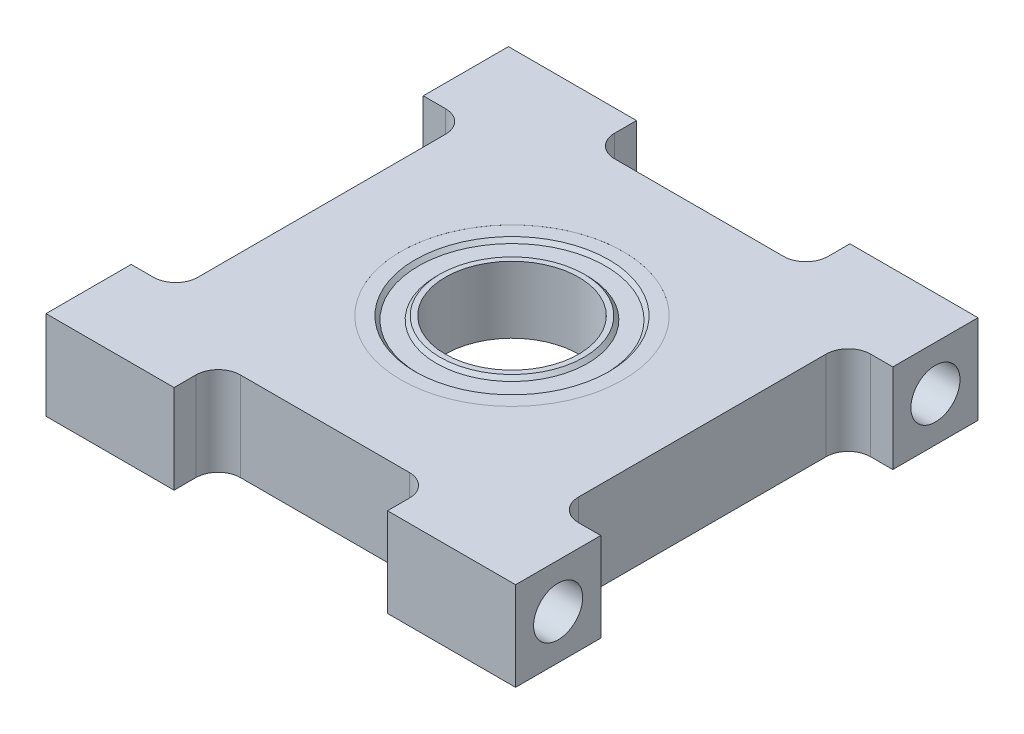
SolidWorks part; units mm, degrees
material "6061 Alloy"
ref_plane "Front Plane" through (0, 0, 0) normal (0, 0, 1) x (1, 0, 0)
ref_plane "Top Plane" through (0, 0, 0) normal (0, 1, 0) x (1, 0, 0)
ref_plane "Right Plane" through (0, 0, 0) normal (1, 0, 0) x (0, 0, -1)
sketch "Sketch1" plane through (0, 0, 0) normal (0, 1, 0) x (1, 0, 0)
  line L0 (-16.764, 0) -> (16.764, 0) construction
  line L1 (-16.764, -16.51) -> (-7.62, -16.51)
  line L2 (-16.764, -16.51) -> (-16.764, -10.4267)
  line L3 (-16.764, 16.51) -> (-7.62, 16.51)
  line L4 (16.764, -16.51) -> (16.764, -10.4267)
  line L5 (-16.764, -16.51) -> (16.764, 16.51) construction
  line L6 (-16.764, 16.51) -> (16.764, -16.51) construction
  line L7 (0, 16.51) -> (0, -16.51) construction
  line L8 (-7.62, -16.51) -> (-7.62, -14.9479)
  line L9 (-6.0325, -13.3604) -> (6.0325, -13.3604)
  line L10 (7.62, -14.9479) -> (7.62, -16.51)
  line L11 (7.62, -16.51) -> (16.764, -16.51)
  line L12 (7.62, 14.9479) -> (7.62, 16.51)
  line L13 (-6.0325, 13.3604) -> (6.0325, 13.3604)
  line L14 (-7.62, 16.51) -> (-7.62, 14.9479)
  line L15 (7.62, 16.51) -> (16.764, 16.51)
  line L16 (-16.764, 10.4267) -> (-15.1765, 10.4267)
  line L17 (-13.589, 8.8392) -> (-13.589, -8.8392)
  line L18 (-15.1765, -10.4267) -> (-16.764, -10.4267)
  line L19 (-16.764, 10.4267) -> (-16.764, 16.51)
  line L20 (15.1765, -10.4267) -> (16.764, -10.4267)
  line L21 (13.589, 8.8392) -> (13.589, -8.8392)
  line L22 (16.764, 10.4267) -> (15.1765, 10.4267)
  line L23 (16.764, 10.4267) -> (16.764, 16.51)
  arc A0 (6.0325, -13.3604) -> (7.62, -14.9479) centre (6.0325, -14.9479) cw
  arc A1 (-7.62, -14.9479) -> (-6.0325, -13.3604) centre (-6.0325, -14.9479) cw
  arc A2 (-7.62, 14.9479) -> (-6.0325, 13.3604) centre (-6.0325, 14.9479) ccw
  arc A3 (6.0325, 13.3604) -> (7.62, 14.9479) centre (6.0325, 14.9479) ccw
  arc A4 (-13.589, -8.8392) -> (-15.1765, -10.4267) centre (-15.1765, -8.8392) cw
  arc A5 (-15.1765, 10.4267) -> (-13.589, 8.8392) centre (-15.1765, 8.8392) cw
  arc A6 (15.1765, 10.4267) -> (13.589, 8.8392) centre (15.1765, 8.8392) ccw
  arc A7 (13.589, -8.8392) -> (15.1765, -10.4267) centre (15.1765, -8.8392) ccw
  circle A8 centre (0, 0) radius 7.62
  point P0 (0, 0)
  dimension "D6" = 1.5875
  dimension "D10" = 1.5875
  dimension "D11" = 15.24
  dimension "D1" = 33.02
  dimension "D2" = 33.528
  dimension "D3" = 15.24
  dimension "D4" = 7.62
  dimension "D5" = 3.1496
  dimension "D7" = 20.8534
  dimension "D8" = 10.4267
  dimension "D9" = 3.175
extrude "Boss-Extrude1" add sketch "Sketch1" along normal blind 6.35
sketch "Sketch2" plane through (0, 6.35, 0) normal (0, 1, 0) x (1, 0, 0)
  circle A0 centre (0, 0) radius 7.9375
  dimension "D1" = 15.875
extrude "Cut-Extrude1" cut sketch "Sketch2" against normal blind 4.7625
ref_plane "Plane1" through (0, 1.5875, 0) normal (0, 1, 0) x (-1, 0, 0)
sketch "Sketch3" plane through (0, 1.5875, 0) normal (0, 1, 0) x (-1, 0, 0)
  circle A0 centre (0, 0) radius 7.9375
  circle A1 centre (0, 0) radius 6.6675
  dimension "D2" = 13.335
  dimension "D1" = 1.27
extrude "Boss-Extrude2" add sketch "Sketch3" along normal blind 4.76
chamfer "Chamfer1" distance 0.254 angle 45 2 edges at (0, 1.5875, 6.6675) (0, 6.3475, 6.6675)
sketch "Sketch4" plane through (0, 1.5875, 0) normal (0, 1, 0) x (-1, 0, 0)
  circle A0 centre (0, 0) radius 4.7625
  circle A1 centre (0, 0) radius 5.3975
  dimension "D1" = 9.525
  dimension "D2" = 0.635
extrude "Boss-Extrude3" add sketch "Sketch4" along normal blind 4.76 separate body
chamfer "Chamfer2" distance 0.254 angle 45 2 edges at (0, 1.5875, 5.3975) (0, 6.3475, 5.3975)
ref_plane "Plane2" through (0, 6.0935, 0) normal (0, 1, 0) x (-1, 0, 0)
sketch "Sketch5" plane through (0, 6.0935, 0) normal (0, 1, 0) x (-1, 0, 0)
  circle A0 centre (0, 0) radius 6.6675
  circle A1 centre (0, 0) radius 5.3975
  dimension "D1" = 13.335
  dimension "D2" = 10.795
extrude "Boss-Extrude4" add sketch "Sketch5" against normal blind 4.2545
hole_wizard "#6-32 Tapped Hole1" positions "Sketch9" profile "Sketch8" tap size "#6-32" standard "Ansi Inch"
sketch "Sketch9" plane through (-16.764, 0, 0) normal (-1, 0, 0) x (0, 0, 1)
  line L0 (-13.4704, 3.175) -> (13.4704, 3.175) construction
  line L1 (-13.4704, 3.175) -> (0, 16.6454) construction
  line L2 (13.4704, 3.175) -> (0, 16.6454) construction
  line L3 (-16.51, 0) -> (-10.4267, 0) construction
  point P0 (-13.4704, 3.175)
  point P1 (13.4704, 3.175)
  dimension "D1" = 19.05
  dimension "D2" = 19.05
  dimension "D3" = 3.175
sketch "Sketch8" plane through (-16.764, 3.175, -13.4704) normal (0, 1, 0) x (0, 0, 1)
  line L0 (0, 0) -> (0, 8.7629)
  line L1 (0, 8.7629) -> (1.3525, 7.9502)
  line L2 (1.3525, 7.9502) -> (1.3525, 7.0104)
  line L3 (1.3525, 7.0104) -> (1.7526, 7.0104)
  line L4 (1.7526, 7.0104) -> (1.7526, 0)
  line L5 (1.7526, 0) -> (0, 0)
  line L10 (0, 8.7629) -> (-1.3526, 7.9502) construction
  line L11 (0, -6.35) -> (0, 107.95) construction
  dimension "Tap Drill Dia." = 2.7051
  dimension "Tap Drill Depth" = 7.9502
  dimension "Thread Major Dia." = 3.5052
  dimension "Thread Depth" = 7.0104
  dimension "Drill Angle" = 118
mirror "Mirror1" about plane through (0, 0, 0) normal (1, 0, 0) of "#6-32 Tapped Hole1"
